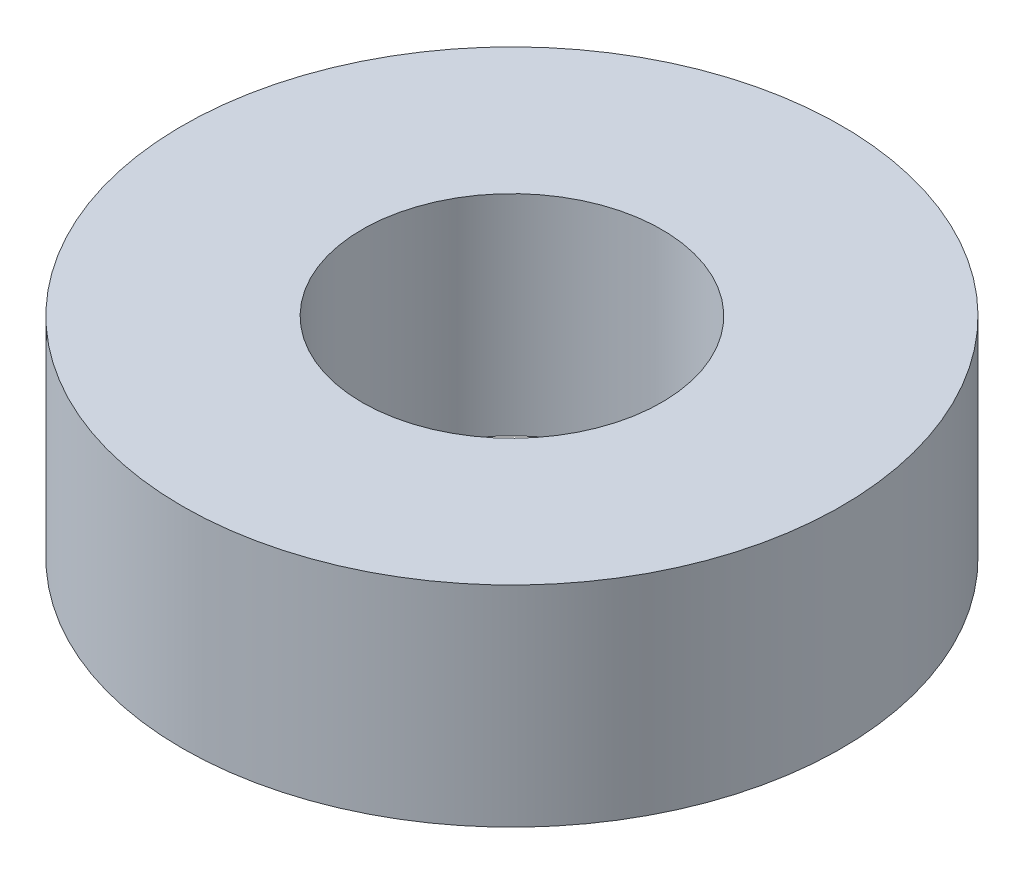
SolidWorks part; units mm, degrees
ref_plane "Front Plane" through (0, 0, 0) normal (0, 0, 1) x (1, 0, 0)
ref_plane "Top Plane" through (0, 0, 0) normal (0, 1, 0) x (1, 0, 0)
ref_plane "Right Plane" through (0, 0, 0) normal (1, 0, 0) x (0, 0, -1)
sketch "Sketch1" plane through (0, 0, 0) normal (0, 1, 0) x (1, 0, 0)
  circle A0 centre (0, 0) radius 17.4625
  circle A1 centre (0, 0) radius 7.9375
  dimension "D1" = 34.925
  dimension "D2" = 15.875
extrude "Boss-Extrude1" add sketch "Sketch1" along normal blind 11.1125
